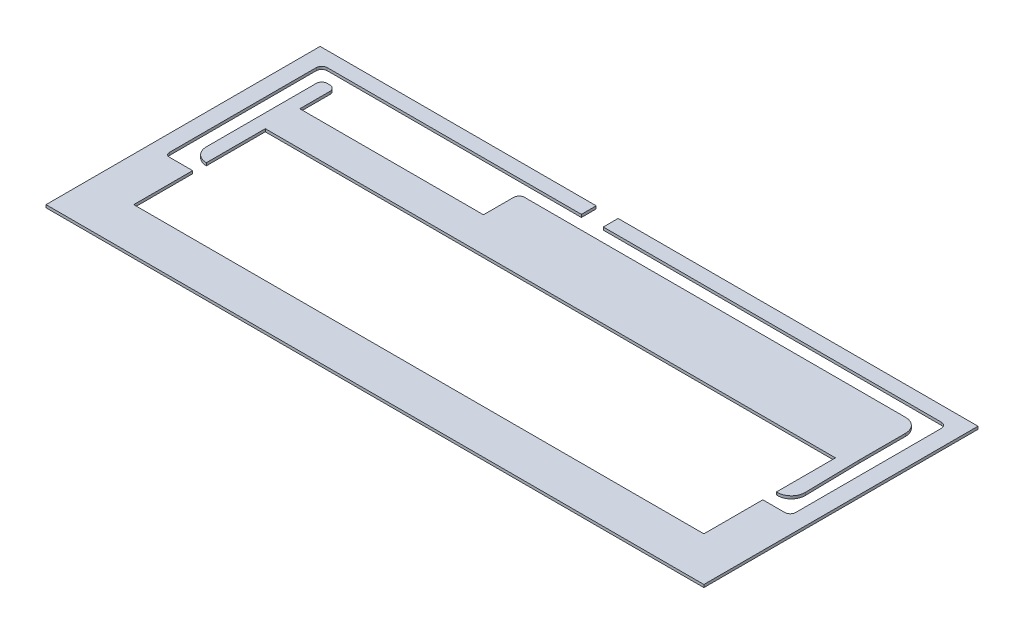
SolidWorks part; units mm, degrees
other "Marca1"
sketch "Croquis6" plane through (483.1, 12, 3.1) normal (0.4175, 0.3737, 0.8283) x (0.8528, 0.1536, -0.4991)
material "Balsa"
ref_plane "Alzado" through (0, 0, 0) normal (0, 0, 1) x (1, 0, 0)
ref_plane "Planta" through (0, 0, 0) normal (0, 1, 0) x (1, 0, 0)
ref_plane "Vista lateral" through (0, 0, 0) normal (1, 0, 0) x (0, 0, -1)
sketch "Croquis1" plane through (0, 0, 0) normal (0, 1, 0) x (1, 0, 0)
  line L0 (0, 0) -> (-3.1, 0) construction
  line L1 (0, 0) -> (480, 0)
  line L2 (0, 0) -> (0, 200)
  line L3 (0, 200) -> (480, 200)
  line L4 (480, 0) -> (480, 200)
  line L5 (0, 0) -> (0, -3.1) construction
  line L6 (-3.1, 0) -> (-3.1, -3.1) construction
  line L7 (-3.1, -3.1) -> (0, -3.1) construction
  line L8 (480, 200) -> (480, 203.1) construction
  line L9 (480, 203.1) -> (483.1, 203.1) construction
  line L11 (-3.1, -3.1) -> (483.1, -3.1)
  line L12 (-3.1, -3.1) -> (-3.1, 203.1)
  line L13 (-3.1, 203.1) -> (483.1, 203.1)
  line L14 (483.1, -3.1) -> (483.1, 203.1)
extrude "Saliente-Extruir1" add sketch "Croquis1" along normal blind 12 contours L1 L4 L3 L2 | L11 L14 L13 L12 L4 L1 L2 L3
sketch "Croquis2" plane through (0, 12, 0) normal (0, 1, 0) x (1, 0, 0)
  line L0 (21.9636, 184.1902) -> (21.9636, 179.1902) construction
  line L1 (17, 184.1902) -> (17, 189.1902) construction
  line L2 (17, 189.1902) -> (16, 189.1902)
  line L3 (28, 184.1902) -> (58, 184.1902) construction
  line L4 (32, 128) -> (448, 128)
  line L6 (32, 32) -> (448, 32)
  line L8 (32, 128) -> (448, 32) construction
  line L9 (32, 32) -> (448, 128) construction
  line L10 (32, 80) -> (17, 80) construction
  line L15 (17, 184.1902) -> (12, 184.1902) construction
  line L16 (28, 184.1902) -> (17, 184.1902) construction
  line L17 (17, 184.1902) -> (17, 80) construction
  line L18 (17, 184.1902) -> (17, 149.1902) construction
  line L19 (12, 185.1902) -> (12, 184.1902)
  line L20 (12, 146.1902) -> (12, 184.1902)
  line L21 (463, 189.1902) -> (464, 189.1902)
  line L22 (17, 80) -> (12, 80) construction
  line L23 (17, 80) -> (17, 75) construction
  line L24 (12, 184.1902) -> (12, 80)
  line L25 (12, 80) -> (12, 78)
  line L26 (15, 75) -> (17, 75)
  line L27 (17, 75) -> (32, 75)
  line L28 (17, 80) -> (21.9636, 80) construction
  line L29 (468, 185.1902) -> (468, 79)
  line L30 (31.9636, 85) -> (32, 85)
  line L31 (463, 189.1902) -> (448, 189.1902)
  line L32 (21.9636, 95) -> (21.9636, 175.1902)
  line L33 (25.9636, 179.1902) -> (28, 179.1902)
  line L34 (58, 184.1902) -> (448, 184.1902) construction
  line L35 (448, 80) -> (463, 80) construction
  line L36 (463, 80) -> (463, 184.1902) construction
  line L37 (463, 184.1902) -> (448, 184.1902) construction
  line L38 (459, 75) -> (459, 85) construction
  line L39 (448.8054, 85) -> (448, 85)
  line L40 (459, 75) -> (448, 75)
  line L41 (458.8036, 95.1927) -> (458.0364, 135)
  line L42 (32, 179.1902) -> (32, 189.1902) construction
  line L43 (448.0364, 125) -> (448, 125)
  line L44 (32, 189.1902) -> (17, 189.1902)
  line L45 (458.0364, 135) -> (458.0364, 169.1902)
  line L46 (464, 75) -> (459, 75)
  line L47 (166, 189.1902) -> (448, 189.1902)
  line L48 (32, 189.1902) -> (166, 189.1902)
  line L50 (32, 153.1902) -> (166, 153.1902)
  line L52 (448.0364, 179.1902) -> (170, 179.1902)
  line L53 (166, 175.1902) -> (166, 153.1902)
  line L54 (32, 175.1902) -> (32, 153.1902)
  line L55 (32, 128) -> (32, 85)
  line L56 (32, 75) -> (32, 32)
  line L57 (32, 85) -> (32, 75)
  line L58 (448, 128) -> (448, 85)
  line L59 (448, 32) -> (448, 75)
  line L60 (448, 85) -> (448, 75)
  line L61 (201.4487, 189.1902) -> (201.4487, 203.1)
  line L62 (-3.1, 203.1) -> (483.1, 203.1) construction
  line L63 (201.4487, 203.1) -> (217.4247, 203.1)
  line L64 (217.4247, 203.1) -> (217.4247, 189.1902)
  arc A0 (458.8036, 95.1927) -> (448.8054, 85) centre (448.8054, 95) cw
  arc A1 (458.0364, 169.1902) -> (448.0364, 179.1902) centre (448.0364, 169.1902) ccw
  arc A2 (21.9636, 95) -> (31.9636, 85) centre (31.9636, 95) ccw
  arc A3 (16, 189.1902) -> (12, 185.1902) centre (16, 185.1902) ccw
  arc A4 (464, 189.1902) -> (468, 185.1902) centre (464, 185.1902) cw
  arc A5 (468, 79) -> (464, 75) centre (464, 79) cw
  arc A6 (170, 179.1902) -> (166, 175.1902) centre (170, 175.1902) ccw
  arc A7 (12, 78) -> (15, 75) centre (15, 78) ccw
  arc A8 (21.9636, 175.1902) -> (25.9636, 179.1902) centre (25.9636, 175.1902) cw
  arc A9 (28, 179.1902) -> (32, 175.1902) centre (28, 175.1902) cw
  point P6 (240, 80)
  dimension "D1" = 10
  dimension "D2" = 4
  dimension "D3" = 4
sketch "Croquis3" plane through (0, 12, 0) normal (0, 1, 0) x (1, 0, 0)
  line L1 (0, 0) -> (480, 0)
  line L2 (0, 0) -> (0, 200)
  line L3 (0, 200) -> (480, 200)
  line L4 (480, 0) -> (480, 200)
  line L5 (-3.1, -3.1) -> (483.1, -3.1)
  line L6 (-3.1, -3.1) -> (-3.1, 203.1)
  line L7 (-3.1, 203.1) -> (483.1, 203.1)
  line L8 (483.1, -3.1) -> (483.1, 203.1)
extrude "Cortar-Extruir1" cut sketch "Croquis3" against normal blind 5
extrude "Cortar-Extruir3" cut sketch "Croquis2" against normal blind 8
sketch "Croquis4" plane through (0, 12, 0) normal (0, 1, 0) x (1, 0, 0)
  line L0 (32, 128) -> (32, 134)
  line L1 (32, 134) -> (52, 134)
  line L2 (52, 134) -> (52, 128)
  line L3 (32, 128) -> (448, 128) construction
  line L4 (52, 128) -> (32, 128)
  line L5 (240, 32) -> (240, 128) construction
  line L6 (32, 32) -> (448, 32) construction
  line L7 (32, 128) -> (448, 128) construction
  line L8 (240, 80) -> (282.8706, 80) construction
  line L9 (428, 134) -> (428, 128)
  line L10 (448, 128) -> (448, 134)
  line L11 (428, 128) -> (448, 128)
  line L12 (448, 134) -> (428, 134)
  line L13 (448, 32) -> (448, 26)
  line L14 (428, 32) -> (448, 32)
  line L15 (448, 26) -> (428, 26)
  line L16 (428, 26) -> (428, 32)
  line L17 (52, 26) -> (52, 32)
  line L18 (52, 32) -> (32, 32)
  line L19 (32, 26) -> (52, 26)
  line L20 (32, 32) -> (32, 26)
  line L21 (32, 75) -> (32, 69)
  line L22 (32, 75) -> (32, 32) construction
  line L23 (12, 80) -> (6, 80) construction
  line L24 (12, 185.1902) -> (12, 78) construction
  line L25 (32, 69) -> (6, 69)
  line L26 (16, 189.1902) -> (16, 195.1902) construction
  line L27 (6, 69) -> (6, 80)
  line L28 (6, 80) -> (6, 195.1902)
  line L29 (6, 195.1902) -> (16, 195.1902)
  line L30 (32, 189.1902) -> (32, 195.1902)
  line L31 (16, 189.1902) -> (201.4487, 189.1902) construction
  line L32 (32, 195.1902) -> (16, 195.1902)
  line L33 (16, 189.1902) -> (32, 189.1902)
  line L34 (12, 185.1902) -> (12, 80)
  line L35 (32, 75) -> (15, 75)
  line L36 (12, 80) -> (12, 78)
  line L37 (31.9636, 85) -> (32, 128)
  line L38 (32, 175.1902) -> (32, 134)
  line L39 (25.9636, 179.1902) -> (28, 179.1902)
  line L40 (21.9636, 175.1902) -> (21.9636, 95)
  line L41 (99, 153.1902) -> (99, 189.1902) construction
  line L42 (32, 153.1902) -> (52, 153.1902)
  line L43 (32, 153.1902) -> (32, 147.1902)
  line L44 (32, 147.1902) -> (52, 147.1902)
  line L45 (52, 153.1902) -> (52, 147.1902)
  line L46 (32, 153.1902) -> (166, 153.1902) construction
  line L47 (99, 171.1902) -> (116.5825, 171.1902) construction
  line L48 (52, 189.1902) -> (52, 195.1902)
  line L49 (32, 195.1902) -> (52, 195.1902)
  line L50 (32, 189.1902) -> (52, 189.1902)
  line L51 (146, 189.1902) -> (146, 195.1902)
  line L52 (166, 189.1902) -> (146, 189.1902)
  line L53 (166, 195.1902) -> (146, 195.1902)
  line L54 (166, 189.1902) -> (166, 195.1902)
  line L55 (166, 153.1902) -> (146, 153.1902)
  line L56 (166, 153.1902) -> (166, 147.1902)
  line L57 (146, 153.1902) -> (146, 147.1902)
  line L58 (166, 147.1902) -> (146, 147.1902)
  line L59 (468, 185.1902) -> (474, 185.1902) construction
  line L60 (464, 189.1902) -> (464, 195.1902) construction
  line L61 (464, 195.1902) -> (474, 195.1902) construction
  line L62 (166, 147.1902) -> (474, 147.1902) construction
  line L63 (448, 75) -> (448, 69) construction
  line L64 (166, 195.1902) -> (474, 195.1902)
  line L65 (166, 195.1902) -> (166, 147.1902)
  line L66 (166, 147.1902) -> (474, 147.1902)
  line L67 (474, 195.1902) -> (474, 147.1902)
  line L68 (448, 75) -> (448, 32) construction
  line L70 (474, 147.1902) -> (448, 147.1902)
  line L71 (474, 147.1902) -> (474, 69)
  line L72 (474, 69) -> (448, 69)
  line L73 (448, 147.1902) -> (448, 69)
  arc A0 (16, 189.1902) -> (12, 185.1902) centre (16, 185.1902) ccw
  arc A1 (12, 78) -> (15, 75) centre (15, 78) ccw
  arc A2 (21.9636, 95) -> (31.9636, 85) centre (31.9636, 95) ccw construction
  arc A3 (28, 179.1902) -> (32, 175.1902) centre (28, 175.1902) cw
  arc A4 (21.9636, 175.1902) -> (25.9636, 179.1902) centre (25.9636, 175.1902) cw
  arc A5 (21.9636, 95) -> (31.9636, 85) centre (31.9636, 95) ccw
  line M14 (32, 128) -> (448, 128)
  line M15 (448, 128) -> (448, 85)
  line M16 (448, 85) -> (448.8054, 85)
  arc M17 (448.8054, 85) -> (458.8036, 95.1927) centre (448.8054, 95) ccw
  line M18 (458.8036, 95.1927) -> (458.0364, 135)
  line M19 (458.0364, 135) -> (458.0364, 169.1902)
  arc M20 (458.0364, 169.1902) -> (448.0364, 179.1902) centre (448.0364, 169.1902) ccw
  line M21 (448.0364, 179.1902) -> (170, 179.1902)
  arc M22 (170, 179.1902) -> (166, 175.1902) centre (170, 175.1902) ccw
  line M23 (166, 175.1902) -> (166, 153.1902)
  line M24 (166, 153.1902) -> (32, 153.1902)
  line M25 (32, 153.1902) -> (32, 175.1902)
  arc M26 (32, 175.1902) -> (28, 179.1902) centre (28, 175.1902) ccw
  line M27 (28, 179.1902) -> (25.9636, 179.1902)
  arc M28 (25.9636, 179.1902) -> (21.9636, 175.1902) centre (25.9636, 175.1902) ccw
  line M29 (21.9636, 175.1902) -> (21.9636, 95)
  arc M30 (21.9636, 95) -> (31.9636, 85) centre (31.9636, 95) ccw
extrude "Cortar-Extruir4" cut sketch "Croquis4" against normal blind 3 contours L38 L37 L0 M25 M26 M27 M28 M29 M30 | L2 L1 L0 M14 | L45 L38 L44 M24 | A1 L36 L34 A0 L33 L30 L32 L29 L28 L27 L25 L21 L35 | L30 L50 L48 L49 | L18 L20 L19 L17 | L52 L54 L53 L51 | L58 L56 L57 M24 | L56 L66 M19 M20 M21 M22 M23 | L67 L64 L54 L65 L66 M22 M21 M20 M19 | L73 L72 L71 L66 M16 M19 M18 M17 | L10 L12 L9 M14 | L16 L15 L13 L14 | L66 L73 L10 M15 M16 M17 M18 M19
sketch "Croquis5" plane through (0, 4, 0) normal (0, 1, 0) x (1, 0, 0)
  line L0 (32.046, 84.9265) -> (32, 75)
  line L2 (32, 75) -> (15, 75)
  line L3 (25.9636, 179.1902) -> (28, 179.1902)
  line L4 (21.9636, 175.1902) -> (21.9636, 95)
  line L5 (32, 175.1902) -> (32, 153.1902)
  line L6 (32, 153.1902) -> (166, 153.1902)
  line L7 (166, 153.1902) -> (166, 175.1902)
  line L8 (170, 179.1902) -> (448.0364, 179.1902)
  line L9 (458.0364, 169.1902) -> (458.8036, 95.1927)
  line L10 (448.8054, 85) -> (448, 85)
  line L11 (448, 85) -> (448, 75)
  line L12 (448, 75) -> (464, 75)
  line L13 (468, 79) -> (468, 185.1902)
  line L14 (468, 185.1902) -> (468, 79) construction
  line L15 (464, 189.1902) -> (217.4247, 189.1902)
  line L16 (217.4247, 189.1902) -> (217.4247, 203.1)
  line L17 (217.4247, 203.1) -> (201.4487, 203.1)
  line L18 (201.4487, 203.1) -> (201.4487, 189.1902)
  line L19 (201.4487, 189.1902) -> (16, 189.1902)
  line L20 (12, 185.1902) -> (12, 78)
  arc A1 (12, 78) -> (15, 75) centre (15, 78) ccw
  arc A2 (25.9636, 179.1902) -> (21.9636, 175.1902) centre (25.9636, 175.1902) ccw
  arc A3 (21.9636, 95) -> (32.046, 84.9265) centre (32.0371, 95) ccw
  arc A4 (28, 179.1902) -> (32, 175.1902) centre (28, 175.1902) cw
  arc A5 (166, 175.1902) -> (170, 179.1902) centre (170, 175.1902) cw
  arc A6 (448.0364, 179.1902) -> (458.0364, 169.1902) centre (448.0364, 169.1902) cw
  arc A7 (448.8054, 85) -> (458.8036, 95.1927) centre (448.7156, 95.0881) ccw
  arc A8 (468, 79) -> (464, 75) centre (464, 79) cw
  arc A9 (468, 185.1902) -> (464, 189.1902) centre (464, 185.1902) ccw construction
  arc A10 (464, 189.1902) -> (468, 185.1902) centre (464, 185.1902) cw
  arc A11 (16, 189.1902) -> (12, 185.1902) centre (16, 185.1902) ccw
extrude "Cortar-Extruir5" cut sketch "Croquis5" against normal blind 2
sketch "Croquis7" plane through (0, 2, 0) normal (0, 1, 0) x (1, 0, 0)
  line L1 (-211.6054, 341.1803) -> (510.3417, 341.1803)
  line L2 (-211.6054, 341.1803) -> (-211.6054, -18.2396)
  line L3 (-211.6054, -18.2396) -> (510.3417, -18.2396)
  line L4 (510.3417, 341.1803) -> (510.3417, -18.2396)
  line L5 (-211.6054, 341.1803) -> (510.3417, -18.2396) construction
  line L6 (-211.6054, -18.2396) -> (510.3417, 341.1803) construction
  point P0 (149.3682, 161.4704)
extrude "Cortar-Extruir6" cut sketch "Croquis7" against normal blind 10
sketch "Croquis8" plane through (0, 4, 0) normal (0, 1, 0) x (1, 0, 0)
  line L1 (32, 128) -> (448, 128)
  line L2 (32, 128) -> (32, 32)
  line L3 (32, 32) -> (448, 32)
  line L4 (448, 128) -> (448, 32)
extrude "Cortar-Extruir7" cut sketch "Croquis8" against normal blind 10
sketch "Croquis9" plane through (0, 9, 0) normal (0, 1, 0) x (1, 0, 0)
  line L1 (512.9567, 229.5955) -> (-18.948, 229.5955)
  line L2 (512.9567, 229.5955) -> (512.9567, -16.7579)
  line L3 (512.9567, -16.7579) -> (-18.948, -16.7579)
  line L4 (-18.948, 229.5955) -> (-18.948, -16.7579)
  point P4 (425.7612, 15.2567)
  point P5 (512.9567, 229.5955)
sketch "Croquis10" plane through (0, 7, 0) normal (0, 1, 0) x (1, 0, 0)
  line L1 (-18.948, 229.5955) -> (512.9567, 229.5955)
  line L2 (-18.948, 229.5955) -> (-18.948, -16.7579)
  line L3 (-18.948, -16.7579) -> (512.9567, -16.7579)
  line L4 (512.9567, 229.5955) -> (512.9567, -16.7579)
ref_plane "Plano1" through (0, 5, 0) normal (0, -1, 0) x (-1, 0, 0)
sketch "Croquis11" plane through (0, 5, 0) normal (0, -1, 0) x (-1, 0, 0)
  line L1 (-512.9567, 229.5955) -> (18.948, 229.5955)
  line L2 (-512.9567, 229.5955) -> (-512.9567, -16.7579)
  line L3 (-512.9567, -16.7579) -> (18.948, -16.7579)
  line L4 (18.948, 229.5955) -> (18.948, -16.7579)
extrude "Cortar-Extruir9" cut sketch "Croquis9" along normal blind 10
extrude "Cortar-Extruir10" cut sketch "Croquis10" against normal blind 10 contours L1 L4 L3 L2
